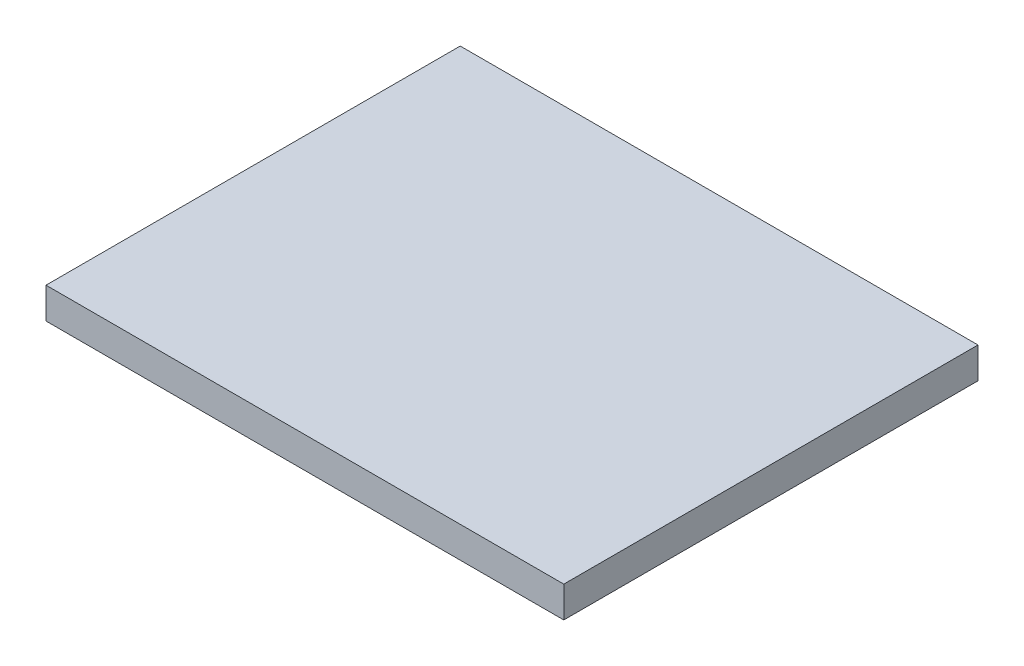
SolidWorks part; units mm, degrees
ref_plane "Front Plane" through (0, 0, 0) normal (0, 0, 1) x (1, 0, 0)
ref_plane "Top Plane" through (0, 0, 0) normal (0, 1, 0) x (1, 0, 0)
ref_plane "Right Plane" through (0, 0, 0) normal (1, 0, 0) x (0, 0, -1)
sketch "Sketch1" plane through (0, 0, 0) normal (0, 1, 0) x (1, 0, 0)
  line L1 (-90.8046, 75.5747) -> (9.1954, 75.5747)
  line L2 (-90.8046, 75.5747) -> (-90.8046, -4.4253)
  line L3 (-90.8046, -4.4253) -> (9.1954, -4.4253)
  line L4 (9.1954, 75.5747) -> (9.1954, -4.4253)
  dimension "D1" = 80
  dimension "D2" = 100
extrude "Boss-Extrude1" add sketch "Sketch1" along normal blind 6
